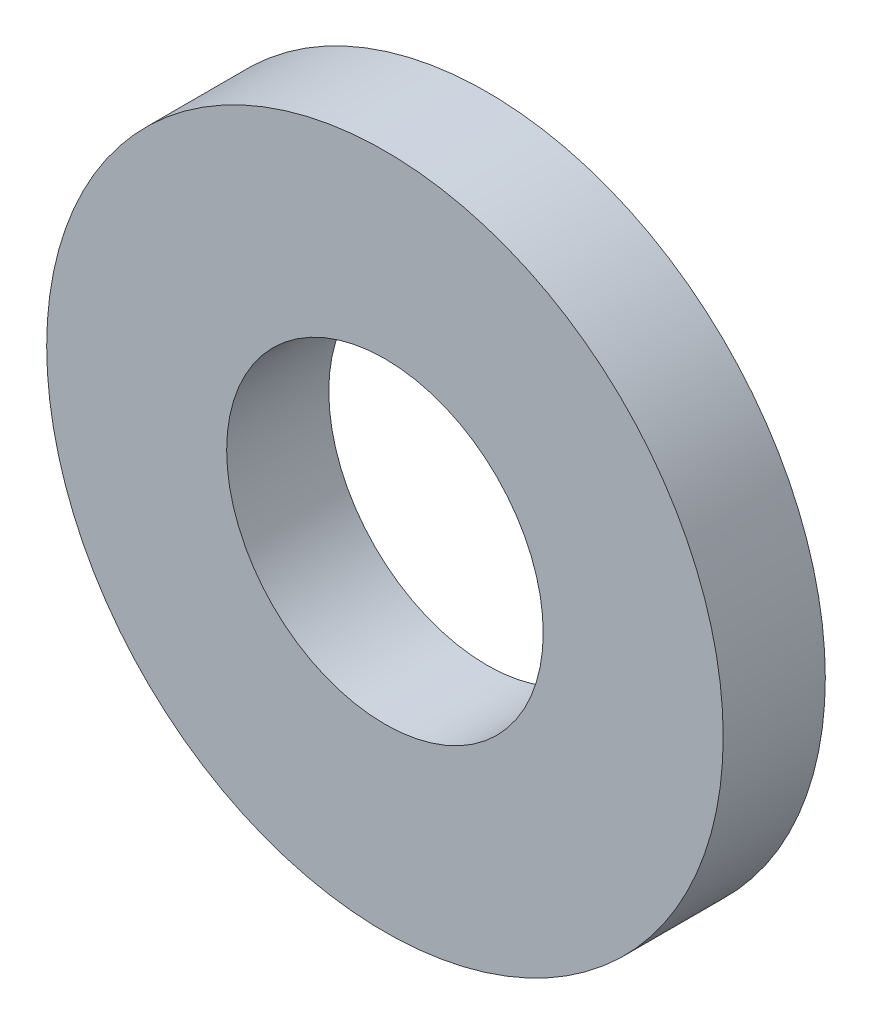
SolidWorks part; units mm, degrees
ref_plane "Front Plane" through (0, 0, 0) normal (0, 0, 1) x (1, 0, 0)
ref_plane "Top Plane" through (0, 0, 0) normal (0, 1, 0) x (1, 0, 0)
ref_plane "Right Plane" through (0, 0, 0) normal (1, 0, 0) x (0, 0, -1)
sketch "Sketch1" plane through (0, 0, 0) normal (0, 0, 1) x (1, 0, 0)
  line L0 (-23.6059, 0) -> (35.2846, 0) construction
  line L1 (0, 27.4574) -> (0, -29.1968) construction
  circle A0 centre (0, 0) radius 66.25
  circle A1 centre (0, 0) radius 25
  dimension "D1" = 132.5
  dimension "D2" = 50
extrude "Boss-Extrude1" add sketch "Sketch1" along normal blind 20 contours A0 | A1
sketch "Sketch4" plane through (0, 0, 20) normal (0, 0, 1) x (1, 0, 0)
  circle A0 centre (0, 0) radius 31
extrude "Cut-Extrude2" cut sketch "Sketch4" against normal through all
